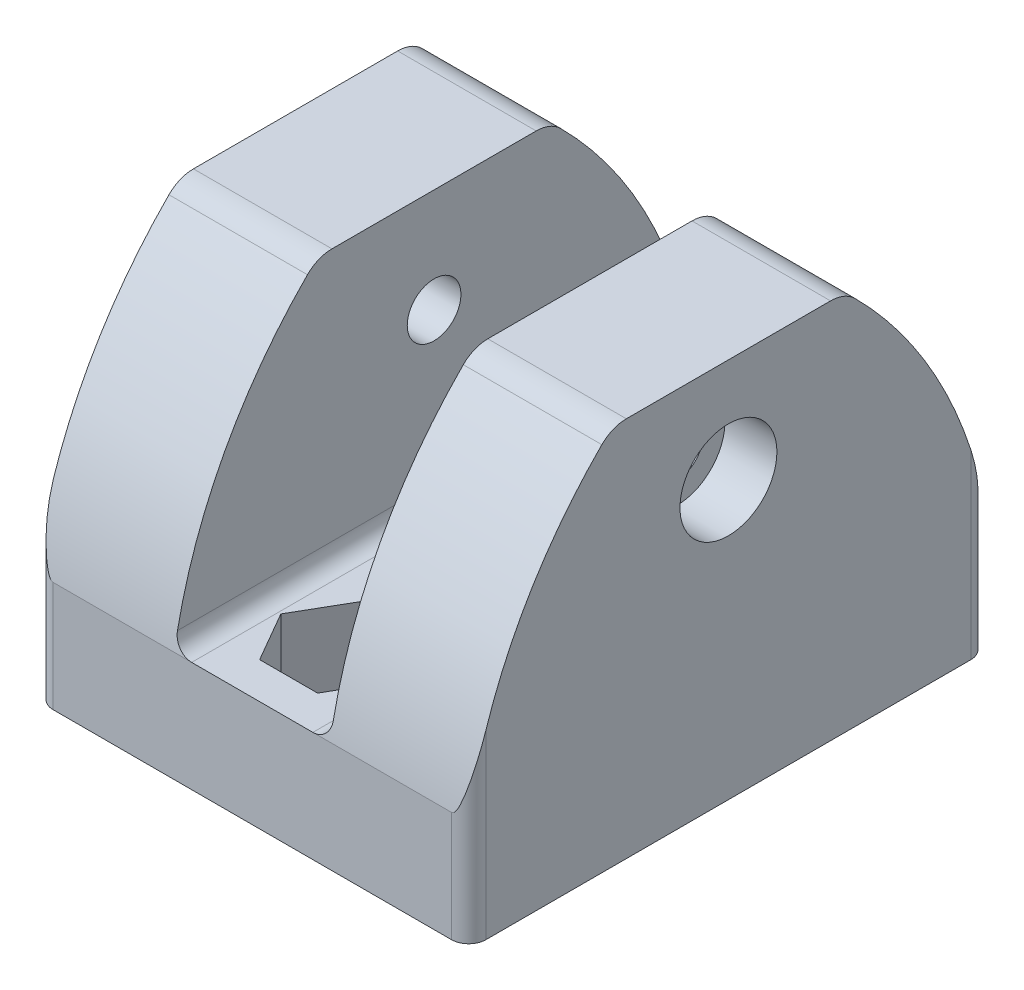
SolidWorks part; units mm, degrees
ref_plane "Alzado" through (0, 0, 0) normal (0, 0, 1) x (1, 0, 0)
ref_plane "Planta" through (0, 0, 0) normal (0, 1, 0) x (1, 0, 0)
ref_plane "Vista lateral" through (0, 0, 0) normal (1, 0, 0) x (0, 0, -1)
sketch "Croquis1" plane through (0, 0, 0) normal (0, 1, 0) x (1, 0, 0)
  line L0 (12.5, 30) -> (12.5, 0) construction
  line L1 (0, 0) -> (25, 0)
  line L2 (0, 0) -> (0, 30)
  line L3 (0, 30) -> (25, 30)
  line L4 (25, 0) -> (25, 30)
  circle A0 centre (12.5, 25) radius 1.55
  circle A1 centre (12.5, 5) radius 1.55
  dimension "D3" = 20
  dimension "D4" = 3.1
  dimension "D1" = 25
  dimension "D2" = 30
  dimension "D5" = 5
extrude "Saliente-Extruir1" add sketch "Croquis1" along normal blind 22
sketch "Croquis2" plane through (0, 0, -30) normal (0, 0, -1) x (-1, 0, 0)
  line L0 (-25, 22) -> (0, 22) construction
  line L1 (-8, 22) -> (-17, 22)
  line L2 (-8, 22) -> (-8, 6.3673)
  line L3 (-8, 6.3673) -> (-17, 6.3673)
  line L4 (-17, 22) -> (-17, 6.3673)
  line L5 (0, 22) -> (0, 0) construction
  dimension "D1" = 9
  dimension "D2" = 8
extrude "Cortar-Extruir1" cut sketch "Croquis2" against normal up to surface (30 mm away) up to face at (12.5, 11, 0)
sketch "Croquis3" plane through (0, 0, 0) normal (-1, 0, 0) x (0, 0, 1)
  line L0 (-15, 0) -> (-15, 22) construction
  line L1 (-30, 0) -> (0, 0) construction
  line L2 (-30, 22) -> (0, 22) construction
  circle A0 centre (-15, 16) radius 1.55
  dimension "D1" = 3.1
  dimension "D2" = 6
extrude "Cortar-Extruir2" cut sketch "Croquis3" against normal up to surface (25 mm away) up to face at (25, 11, -15)
sketch "Croquis4" plane through (0, 0, 0) normal (-1, 0, 0) x (0, 0, 1)
  line L1 (-14.9679, 19.3485) -> (-17.8838, 17.702)
  line L2 (-17.8838, 17.702) -> (-17.9159, 14.3536)
  line L3 (-17.9159, 14.3536) -> (-15.0321, 12.6515)
  line L4 (-15.0321, 12.6515) -> (-12.1162, 14.298)
  line L5 (-12.1162, 14.298) -> (-12.0841, 17.6464)
  line L6 (-12.0841, 17.6464) -> (-14.9679, 19.3485)
  circle A0 centre (-15, 16) radius 2.9 construction
  dimension "D1" = 5.8
extrude "Cortar-Extruir3" cut sketch "Croquis4" against normal blind 2.5
sketch "Croquis5" plane through (25, 0, 0) normal (1, 0, 0) x (0, 0, -1)
  circle A0 centre (15, 16) radius 2.8
  dimension "D1" = 5.6
extrude "Cortar-Extruir4" cut sketch "Croquis5" against normal blind 3
sketch "Croquis6" plane through (0, 6.3673, 0) normal (0, 1, 0) x (1, 0, 0)
  line L1 (15.8486, 25) -> (14.1743, 27.9)
  line L2 (14.1743, 27.9) -> (10.8257, 27.9)
  line L3 (10.8257, 27.9) -> (9.1514, 25)
  line L4 (9.1514, 25) -> (10.8257, 22.1)
  line L5 (10.8257, 22.1) -> (14.1743, 22.1)
  line L6 (14.1743, 22.1) -> (15.8486, 25)
  line L7 (15.8486, 5) -> (14.1743, 7.9)
  line L8 (14.1743, 7.9) -> (10.8257, 7.9)
  line L9 (10.8257, 7.9) -> (9.1514, 5)
  line L10 (9.1514, 5) -> (10.8257, 2.1)
  line L11 (10.8257, 2.1) -> (14.1743, 2.1)
  line L12 (14.1743, 2.1) -> (15.8486, 5)
  circle A0 centre (12.5, 25) radius 2.9 construction
  circle A1 centre (12.5, 5) radius 2.9 construction
  dimension "D1" = 5.8
  dimension "D2" = 5.8
extrude "Cortar-Extruir5" cut sketch "Croquis6" against normal blind 4.5
sketch "Croquis7" plane through (0, 0, 0) normal (-1, 0, 0) x (0, 0, 1)
  line L0 (-15, 0) -> (-15, 22) construction
  line L1 (-30, 0) -> (0, 0) construction
  line L2 (-30, 22) -> (0, 22) construction
  line L3 (-30, 22) -> (-30, 6.37)
  line L4 (-30, 22) -> (-30, 0) construction
  line L5 (-30, 22) -> (-21.7082, 22)
  line L6 (0, 22) -> (-8.2918, 22)
  line L7 (0, 22) -> (0, 6.37)
  circle A0 centre (-15, 16) radius 9
  arc A1 (-30, 6.37) -> (-21.7082, 22) centre (-2.8457, 1.9789) cw
  arc A2 (0, 6.37) -> (-8.2918, 22) centre (-27.1543, 1.9789) ccw
  line M8 (0, 0) -> (0, 22)
  line M9 (0, 22) -> (-30, 22)
  line M10 (-30, 22) -> (-30, 0)
  dimension "D1" = 18
  dimension "D2" = 6.37
extrude "Cortar-Extruir6" cut sketch "Croquis7" against normal up to surface (25 mm away) contours A1 M10 M9 | A2 M8 M9 up to face at (25, 16, -17.8)
fillet "Redondeo1" radius 2 4 edges at (21, 22, -21.7082) (21, 22, -8.2918) (4, 22, -8.2918) (4, 22, -21.7082)
fillet "Redondeo2" radius 1 2 edges at (17, 6.3673, -15) (8, 6.3673, -15)
fillet "Redondeo3" radius 1 4 edges at (25, 3.185, 0) (0, 3.185, 0) (0, 3.185, -30) (25, 3.185, -30)
